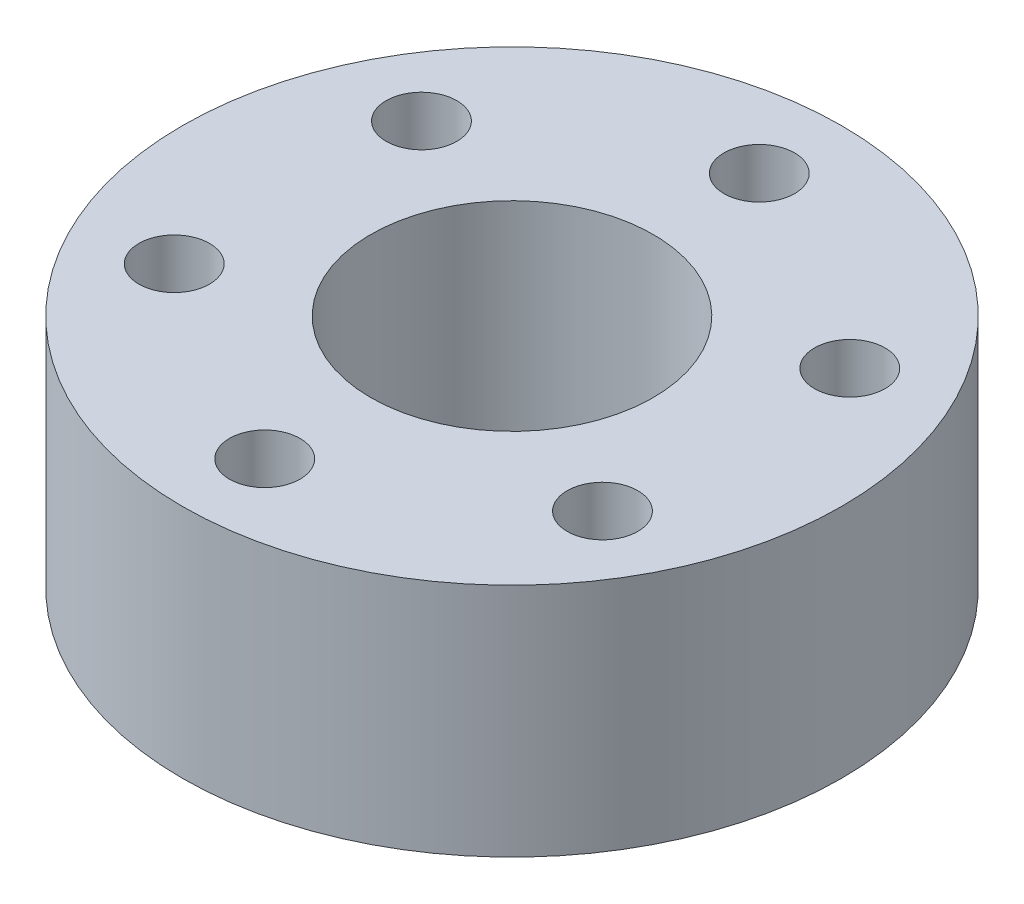
SolidWorks part; units mm, degrees
ref_plane "Front Plane" through (0, 0, 0) normal (0, 0, 1) x (1, 0, 0)
ref_plane "Top Plane" through (0, 0, 0) normal (0, 1, 0) x (1, 0, 0)
ref_plane "Right Plane" through (0, 0, 0) normal (1, 0, 0) x (0, 0, -1)
sketch "Sketch1" plane through (0, 0, 0) normal (0, 1, 0) x (1, 0, 0)
  circle A0 centre (0, 0) radius 14
  dimension "D1" = 28
extrude "Boss-Extrude1" add sketch "Sketch1" along normal blind 10
sketch "Sketch2" plane through (0, 10, 0) normal (0, 1, 0) x (1, 0, 0)
  line L0 (0, 0) -> (0, 50000) construction
  circle A0 centre (0, 0) radius 10.5 construction
  circle A1 centre (0, 10.5) radius 1.5
  circle A2 centre (0, 0) radius 6
  circle A3 centre (9.0933, 5.25) radius 1.5
  circle A4 centre (9.0933, -5.25) radius 1.5
  circle A5 centre (0, -10.5) radius 1.5
  circle A6 centre (-9.0933, -5.25) radius 1.5
  circle A7 centre (-9.0933, 5.25) radius 1.5
  point P18 (0, 0)
  dimension "D1" = 3
  dimension "D2" = 12
  dimension "D3" = 6
extrude "Cut-Extrude1" cut sketch "Sketch2" against normal through all
scale "ｽｹｰﾙ1" scale about centroid uniform scaling yes scale factor 0.894737
